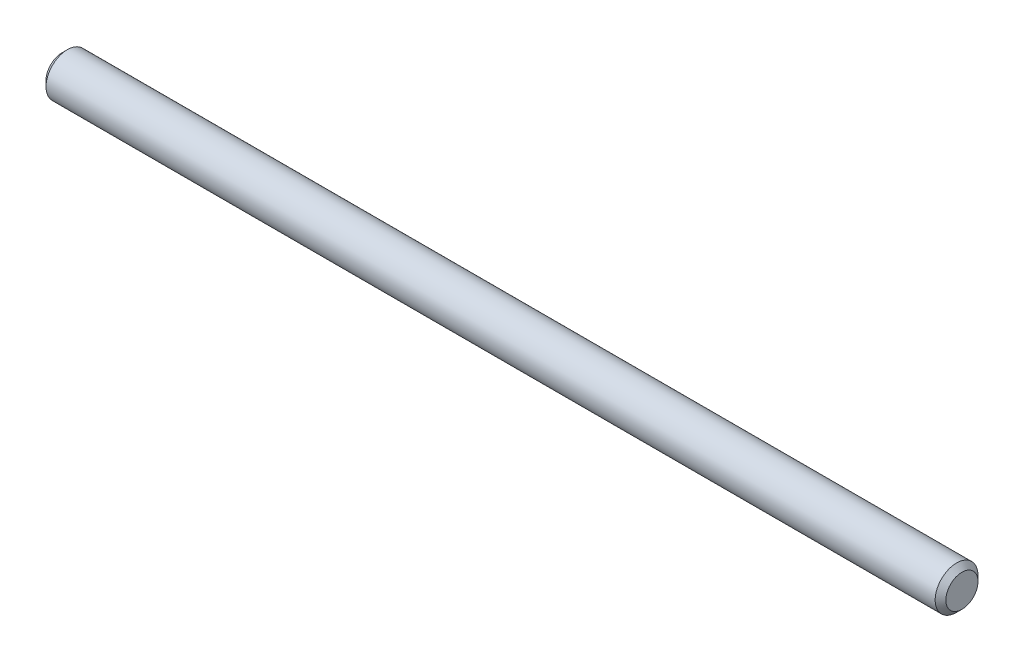
SolidWorks part; units mm, degrees
ref_plane "Front Plane" through (0, 0, 0) normal (0, 0, 1) x (1, 0, 0)
ref_plane "Top Plane" through (0, 0, 0) normal (0, 1, 0) x (1, 0, 0)
ref_plane "Right Plane" through (0, 0, 0) normal (1, 0, 0) x (0, 0, -1)
sketch "Sketch1" plane through (0, 0, 0) normal (1, 0, 0) x (0, 0, -1)
  circle A0 centre (0, 0) radius 2
extrude "Boss-Extrude1" add sketch "Sketch1" along normal blind 84
cosmetic thread "Cosmetic Thread1" parameters "D1"=8, "D2"=3.22
cosmetic thread "Cosmetic Thread2" parameters "D1"=8, "D2"=3.22
chamfer "Chamfer1" distance 0.5 angle 45 1 edges at (0, 0, -2)
chamfer "Chamfer2" distance 0.5 angle 45 1 edges at (84, 0, -2)
